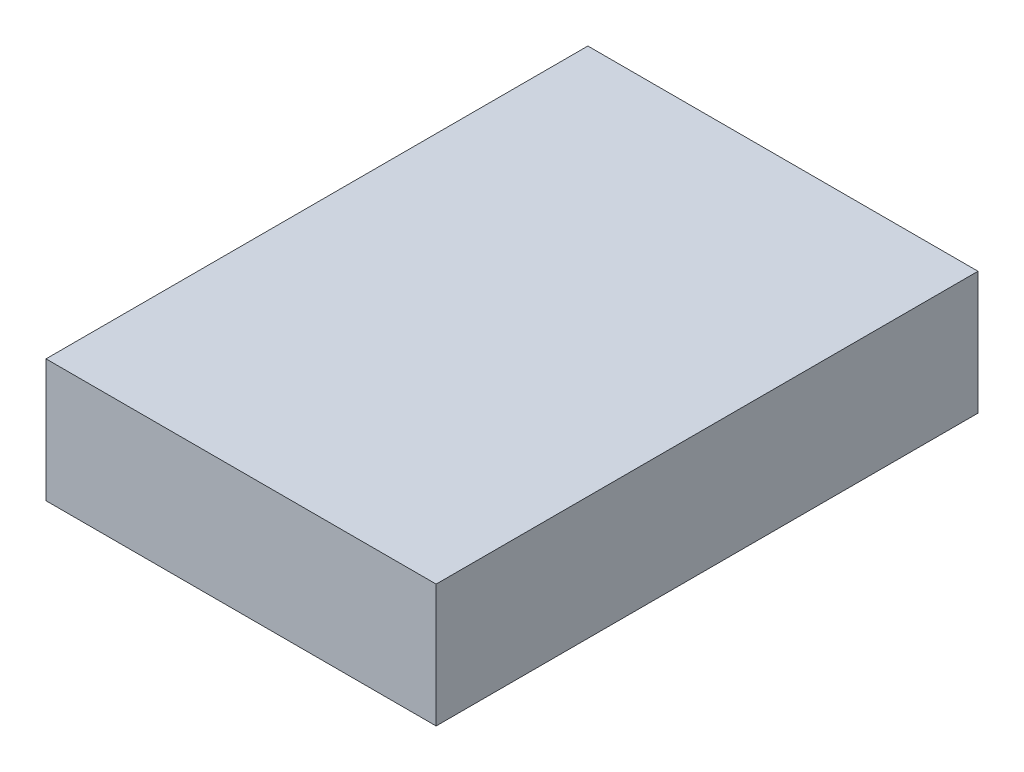
SolidWorks part; units mm, degrees
ref_plane "Front Plane" through (0, 0, 0) normal (0, 0, 1) x (1, 0, 0)
ref_plane "Top Plane" through (0, 0, 0) normal (0, 1, 0) x (1, 0, 0)
ref_plane "Right Plane" through (0, 0, 0) normal (1, 0, 0) x (0, 0, -1)
sketch "Sketch1" plane through (0, 0, 0) normal (0, 1, 0) x (1, 0, 0)
  line L1 (-8.644, 12.6514) -> (9.356, 12.6514)
  line L2 (-8.644, 12.6514) -> (-8.644, -12.3486)
  line L3 (-8.644, -12.3486) -> (9.356, -12.3486)
  line L4 (9.356, 12.6514) -> (9.356, -12.3486)
  dimension "D1" = 25
  dimension "D2" = 18
extrude "Boss-Extrude1" add sketch "Sketch1" along normal blind 5.67
